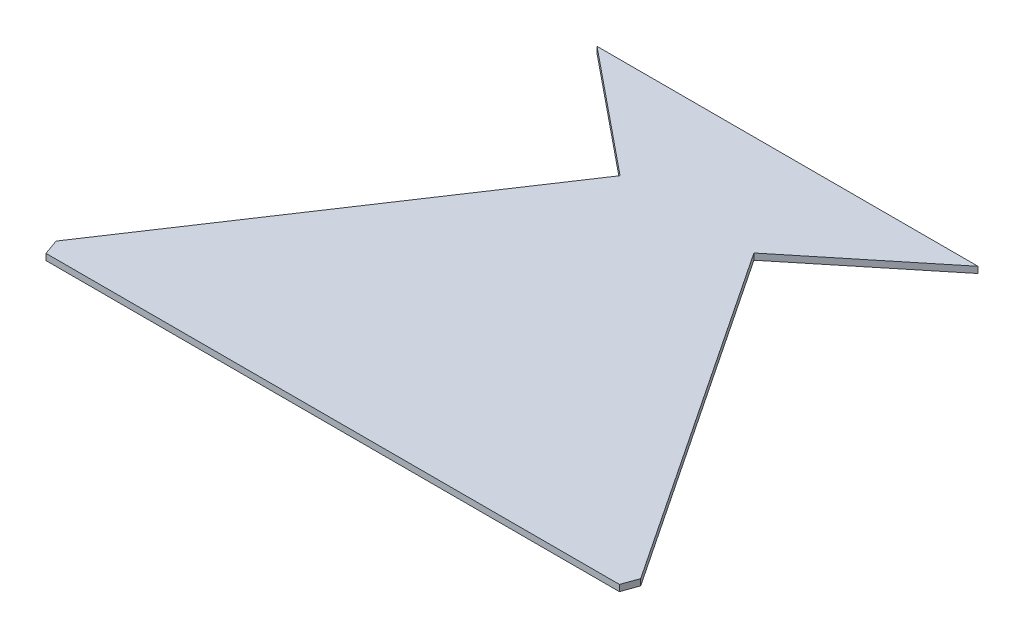
SolidWorks part; units mm, degrees
ref_plane "Plan de face" through (0, 0, 0) normal (0, 0, 1) x (1, 0, 0)
ref_plane "Plan de dessus" through (0, 0, 0) normal (0, 1, 0) x (1, 0, 0)
ref_plane "Plan de droite" through (0, 0, 0) normal (1, 0, 0) x (0, 0, -1)
sketch "Esquisse1" plane through (0, 0, 0) normal (0, 1, 0) x (1, 0, 0)
  line L0 (0, 0) -> (182.4159, 0)
  line L1 (182.4159, 0) -> (184.2001, 4.9864)
  line L2 (184.2001, 4.9864) -> (112.4957, 112.7077)
  line L3 (112.4957, 112.7077) -> (151.8042, 144.6881)
  line L4 (151.8042, 144.6881) -> (30.6117, 144.6881)
  line L5 (30.6117, 144.6881) -> (69.9202, 112.7077)
  line L6 (69.9202, 112.7077) -> (-1.7842, 4.9864)
  line L7 (-1.7842, 4.9864) -> (0, 0)
  point P8 (0, 0)
extrude "Boss.-Extru.1" add sketch "Esquisse1" along normal blind 2
